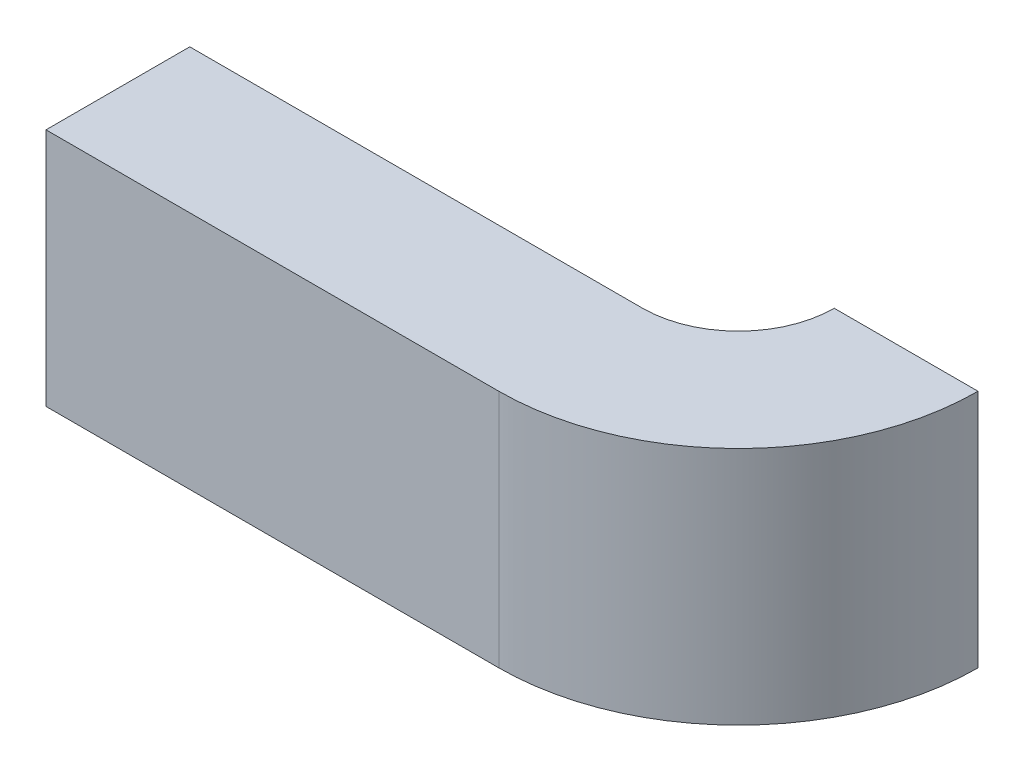
SolidWorks part; units mm, degrees
ref_plane "Front Plane" through (0, 0, 0) normal (0, 0, 1) x (1, 0, 0)
ref_plane "Top Plane" through (0, 0, 0) normal (0, 1, 0) x (1, 0, 0)
ref_plane "Right Plane" through (0, 0, 0) normal (1, 0, 0) x (0, 0, -1)
sketch "Sketch3" plane through (0, 0, 0) normal (0, 1, 0) x (1, 0, 0)
  line L0 (0, 0) -> (0.945, 0) construction
  line L1 (0, -0.15) -> (0.945, -0.15)
  line L2 (0, 0.15) -> (0.945, 0.15)
  line L3 (0, -0.15) -> (0, 0.15)
  line L4 (1.445, 0.35) -> (1.145, 0.35)
  arc A1 (0.945, 0) -> (1.295, 0.35) centre (0.945, 0.35) ccw construction
  arc A2 (0.945, -0.15) -> (1.445, 0.35) centre (0.945, 0.35) ccw
  arc A3 (0.945, 0.15) -> (1.145, 0.35) centre (0.945, 0.35) ccw
  point P0 (1.295, 0.35)
  point P6 (0, 0)
  dimension "D1" = 1.295
  dimension "D2" = 0.35
  dimension "D3" = 0.15
  dimension "D4" = 0.15
extrude "Boss-Extrude1" add sketch "Sketch3" along normal mid plane 0.5
ref_plane "Plane1" through (1.445, 0, 0) normal (1, 0, 0) x (0, 0, -1)
